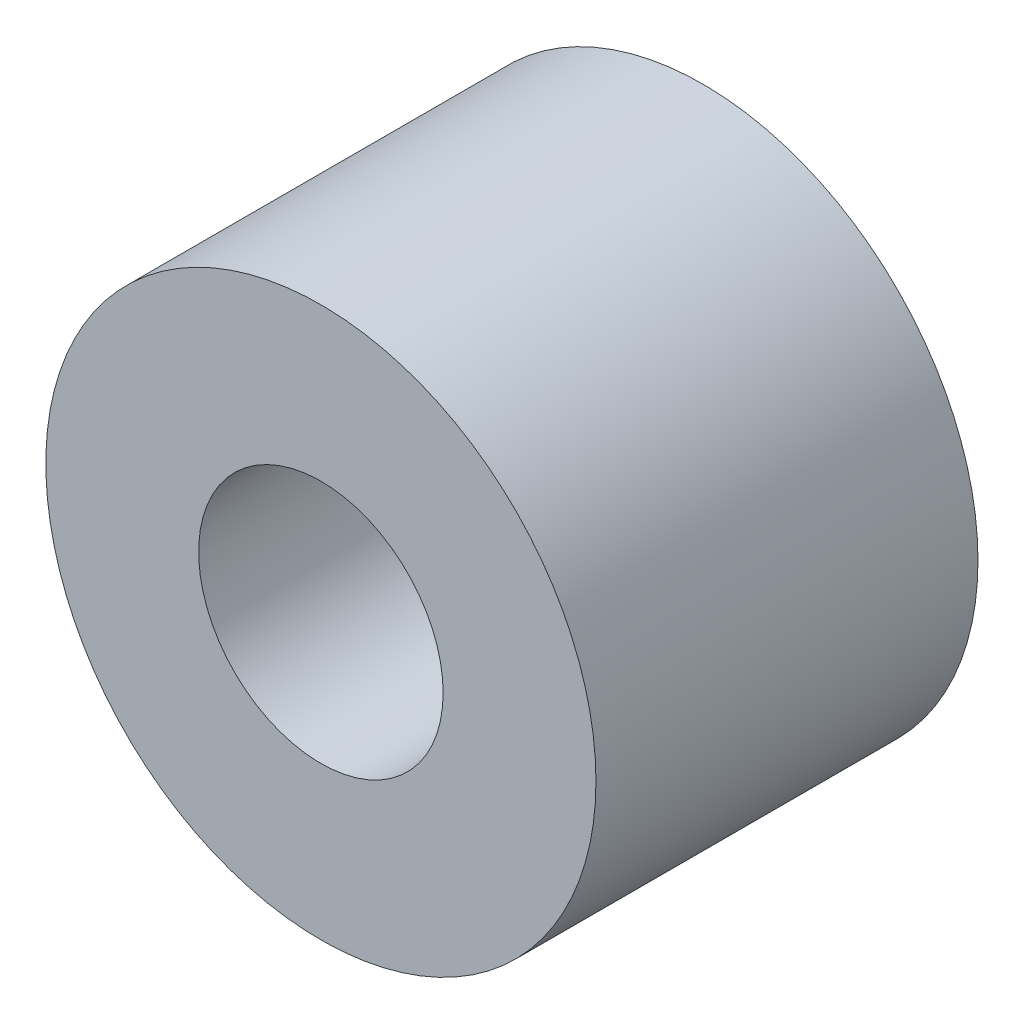
SolidWorks part; units mm, degrees
ref_plane "Front Plane" through (0, 0, 0) normal (0, 0, 1) x (1, 0, 0)
ref_plane "Top Plane" through (0, 0, 0) normal (0, 1, 0) x (1, 0, 0)
ref_plane "Right Plane" through (0, 0, 0) normal (1, 0, 0) x (0, 0, -1)
sketch "Sketch1" plane through (0, 0, 0) normal (0, 0, 1) x (1, 0, 0)
  circle A0 centre (0, 0) radius 1.6
  circle A1 centre (0, 0) radius 3.6
  dimension "D1" = 3.2
  dimension "D2" = 2
extrude "Boss-Extrude1" add sketch "Sketch1" along normal blind 5
